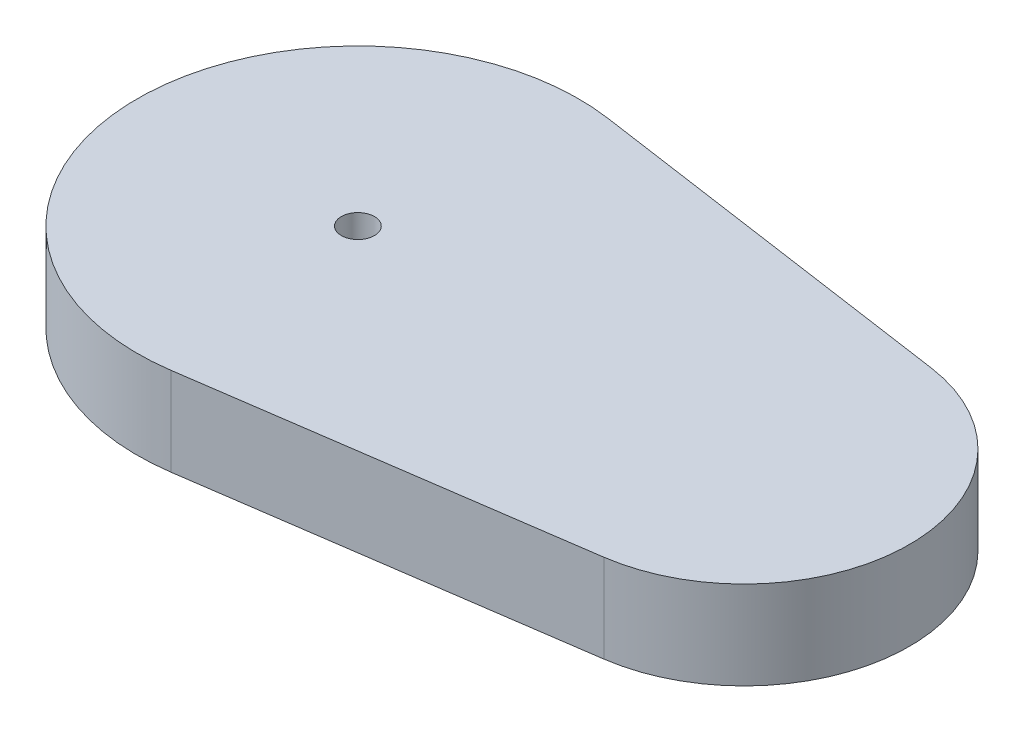
SolidWorks part; units mm, degrees
ref_plane "Front Plane" through (0, 0, 0) normal (0, 0, 1) x (1, 0, 0)
ref_plane "Top Plane" through (0, 0, 0) normal (0, 1, 0) x (1, 0, 0)
ref_plane "Right Plane" through (0, 0, 0) normal (1, 0, 0) x (0, 0, -1)
sketch "Sketch1" plane through (0, 0, 0) normal (0, 1, 0) x (1, 0, 0)
  line L0 (0, 0) -> (14, 0) construction
  line L6 (1.1429, -7.9179) -> (14.8571, -5.9385)
  line L8 (1.1429, 7.9179) -> (14.8571, 5.9385)
  line L11 (14, 0) -> (20, 0) construction
  circle A0 centre (0, 0) radius 0.6
  arc A1 (1.1429, 7.9179) -> (1.1429, -7.9179) centre (0, 0) ccw
  arc A2 (14.8571, 5.9385) -> (14.8571, -5.9385) centre (14, 0) cw
  dimension "D1" = 1.2
  dimension "D2" = 20
  dimension "D5" = 8
  dimension "D6" = 6
  dimension "D3" = 8
sketch "Sketch2" plane through (0, 0, 0) normal (0, 0, 1) x (1, 0, 0)
  line L0 (0, 0) -> (0, 3.2) construction
  dimension "D1" = 3.2
extrude "Boss-Extrude1" add sketch "Sketch1" along normal up to vertex (3.2 mm away) up to point (0, 3.2, 0)
equation "\"glass_width\"= 150"
equation "\"glass_height\"= 100"
equation "\"glass_thickness\"= 4"
equation "\"brood_space\"= 42"
equation "\"t1\"= 6"
equation "\"t2\"= 3.2"
equation "\"box_depth\"= \"brood_space\" + \"glass_thickness\" + \"glass_thickness\" + \"t2\" + \"t2\""
equation "\"box_width\"= \"glass_width\" + \"t1\" + \"t1\""
equation "\"food_height\"= 70"
equation "\"box_height\"= \"glass_height\" + ( \"t1\" * 3 ) + \"food_height\""
equation "\"D1@Sketch2\"=\"t2\""
